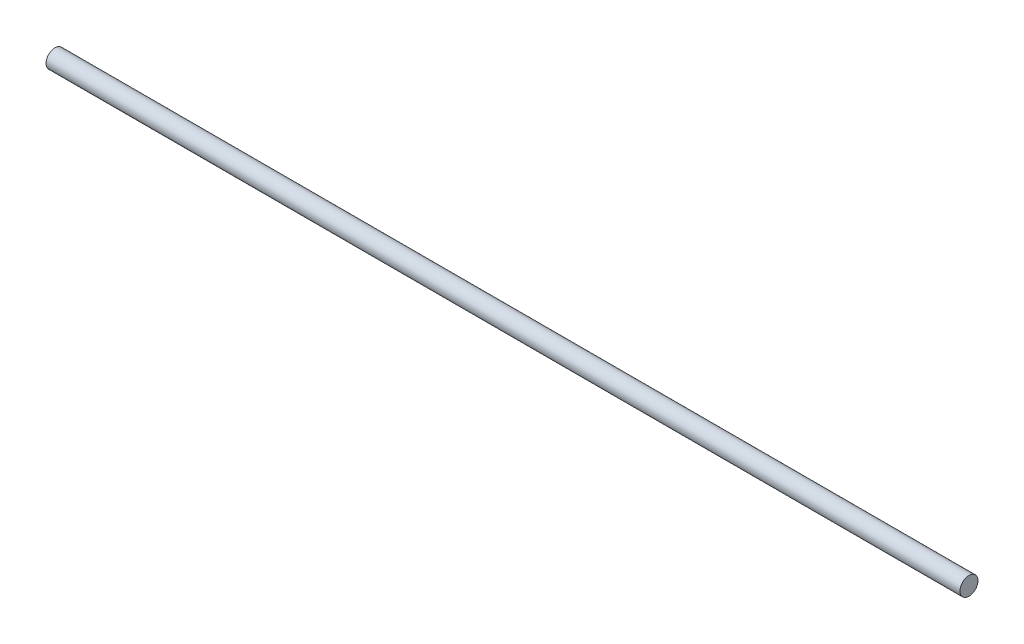
SolidWorks part; units mm, degrees
ref_plane "Front Plane" through (0, 0, 0) normal (0, 0, 1) x (1, 0, 0)
ref_plane "Top Plane" through (0, 0, 0) normal (0, 1, 0) x (1, 0, 0)
ref_plane "Right Plane" through (0, 0, 0) normal (1, 0, 0) x (0, 0, -1)
sketch "Sketch1" plane through (0, 0, 0) normal (1, 0, 0) x (0, 0, -1)
  circle A0 centre (0, 0) radius 4
  dimension "D1" = 8
extrude "Boss-Extrude1" add sketch "Sketch1" along normal mid plane 405
